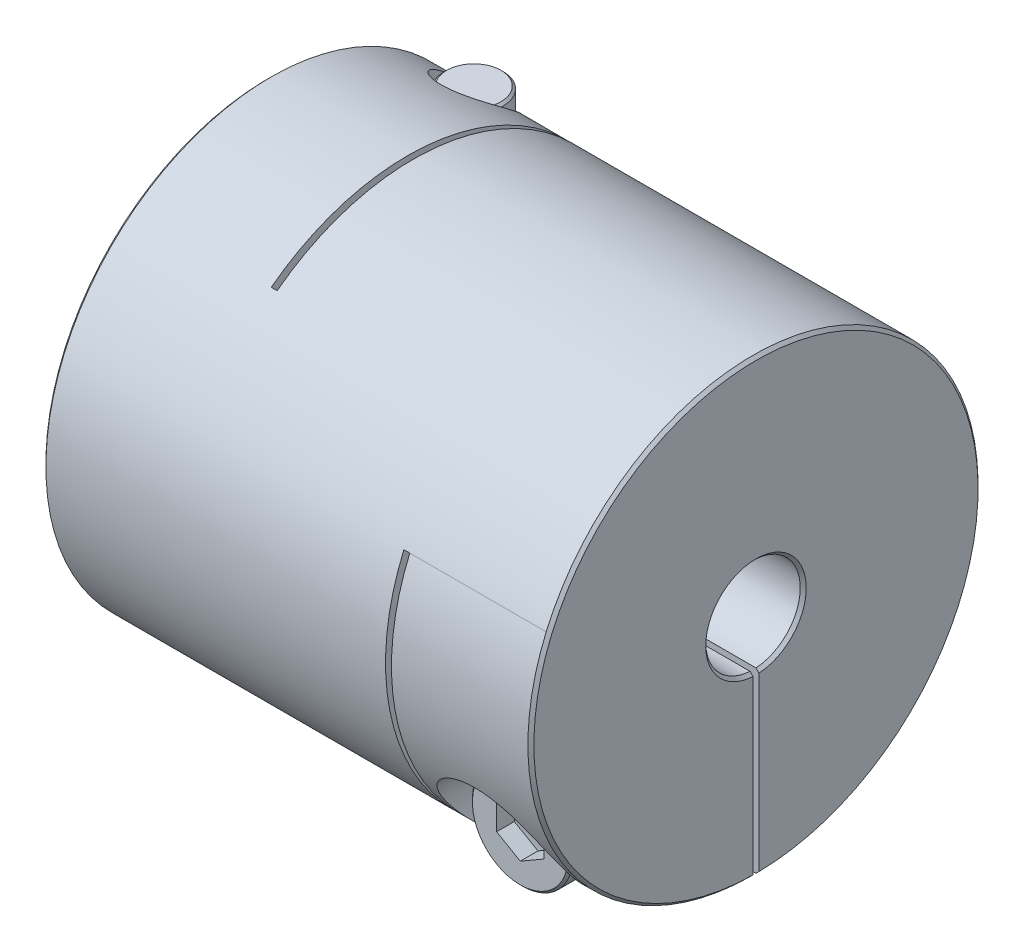
SolidWorks part; units mm, degrees
ref_plane "Front Plane" through (0, 0, 0) normal (0, 0, 1) x (1, 0, 0)
ref_plane "Top Plane" through (0, 0, 0) normal (0, 1, 0) x (1, 0, 0)
ref_plane "Right Plane" through (0, 0, 0) normal (1, 0, 0) x (0, 0, -1)
sketch "Sketch1" plane through (0, 0, 0) normal (1, 0, 0) x (0, 0, -1)
  circle A0 centre (0, 0) radius 19.05
  dimension "dim D" = 38.1
extrude "Boss-Extrude1" add sketch "Sketch1" along normal mid plane 41.3
sketch "Sketch2" plane through (20.65, 0, 0) normal (1, 0, 0) x (0, 0, -1)
  circle A0 centre (0, 0) radius 4
  dimension "dim D1" = 8
extrude "Cut-Extrude1" cut sketch "Sketch2" against normal through all
chamfer "Chamfer1" distance 0.254 angle 45 4 edges at (-20.65, 0, -4) (-20.65, 0, -19.05) (20.65, 0, -19.05) (20.65, 0, -4)
ref_plane "Plane2" through (0, -19.05, 0) normal (0, -1, 0) x (1, 0, 0)
ref_plane "L1" through (-14.75, 0, 0) normal (-1, 0, 0) x (0, 0, 1)
sketch "Sketch4" plane through (0, -19.05, 0) normal (0, -1, 0) x (1, 0, 0)
  line L0 (-20.396, -19.05) -> (20.396, -19.05) construction
  line L1 (-8.85, -19.05) -> (-8.35, -19.05)
  line L2 (-8.85, -19.05) -> (-8.85, 11.525)
  line L3 (-8.85, 11.525) -> (-8.35, 11.525)
  line L4 (-8.35, -19.05) -> (-8.35, 11.525)
  line L5 (-8.85, 4) -> (-8.85, 19.05) construction
  line L6 (20.396, 4) -> (-20.396, 4) construction
  line L7 (20.396, 19.05) -> (-20.396, 19.05) construction
  line L10 (-8.85, 11.525) -> (-20.65, 11.525) construction
  line L11 (-20.65, 18.796) -> (-20.65, -18.796) construction
  line L12 (-14.75, 10.2256) -> (-14.75, -10.2256) construction
  point P16 (-14.75, 11.525)
  dimension "D1" = 0.5
extrude "Cut-Extrude2" cut sketch "Sketch4" against normal through all
ref_plane "Plane4" through (0, 0, -19.05) normal (0, 0, -1) x (-1, 0, 0)
sketch "Sketch7" plane through (0, 0, -19.05) normal (0, 0, -1) x (-1, 0, 0)
  line L1 (-8.35, -19.05) -> (-8.85, -19.05)
  line L2 (-8.85, -19.05) -> (-8.85, 7.525)
  line L3 (-8.85, 7.525) -> (-8.35, 7.525)
  line L4 (-8.35, -19.05) -> (-8.35, 7.525)
  line L5 (20.65, 8.6487) -> (14.75, 8.6487) construction
  line L7 (-10.505, -19.05) -> (10.505, -19.05) construction
  line L8 (-20.396, -4) -> (8.35, -4) construction
  line L9 (20.65, -18.796) -> (20.65, 18.796) construction
  line L10 (-20.396, -4) -> (8.35, -4) construction
  line L11 (8.35, 15.1683) -> (8.85, 15.1683) construction
  line L12 (-8.85, 7.525) -> (-8.85, -19.05) construction
  line L14 (-20.396, -4) -> (8.35, -4) construction
  line L16 (-20.396, -4) -> (8.35, -4) construction
  line L17 (8.85, -19.05) -> (20.396, -19.05) construction
  line L18 (14.75, -10.2256) -> (14.75, 10.2256) construction
  line L19 (-20.396, -19.05) -> (-20.396, 19.05) construction
  line L20 (-20.65, 7.525) -> (-14.75, 7.525) construction
  line L21 (-20.65, 18.796) -> (-20.65, -18.796) construction
  line L22 (-14.75, 7.525) -> (-8.85, 7.525) construction
  line L23 (-20.396, -19.05) -> (-20.396, 19.05) construction
  line L24 (-20.396, -4) -> (-20.396, 19.05) construction
  line L25 (-20.396, -4) -> (8.35, -4) construction
  point P23 (-8.85, 7.525)
  point P33 (-20.396, 7.525)
extrude "Cut-Extrude3" cut sketch "Sketch7" against normal through all
sketch "Sketch8" plane through (0, 0, 0) normal (0, 1, 0) x (1, 0, 0)
  line L0 (-8.85, -11.525) -> (-8.85, 19.05) construction
  line L1 (-20.65, 19.05) -> (-8.85, 19.05)
  line L2 (-20.65, 19.05) -> (-20.65, 0)
  line L3 (-20.65, 0) -> (-8.85, 0)
  line L4 (-8.85, 19.05) -> (-8.85, 0)
  line L5 (10.505, 19.05) -> (-10.505, 19.05) construction
  line L6 (-20.65, 18.796) -> (-20.65, -18.796) construction
extrude "Cut-Extrude5" cut sketch "Sketch8" against normal mid plane 0.5
sketch "Sketch13" plane through (0, 0, 0) normal (0, 0, 1) x (1, 0, 0)
  line L0 (20.65, -18.796) -> (20.65, 18.796) construction
  line L1 (8.85, -19.05) -> (20.65, -19.05)
  line L2 (8.85, -19.05) -> (8.85, 0)
  line L3 (8.85, 0) -> (20.65, 0)
  line L4 (20.65, -19.05) -> (20.65, 0)
extrude "Cut-Extrude6" cut sketch "Sketch13" against normal mid plane 0.5
hole_wizard "CBORE for M5 SHCS1" positions "Sketch12" profile "Sketch11" counterbore size "M5" standard "Ansi Metric" end condition through all
sketch "Sketch12" plane through (0, -19.05, 0) normal (0, -1, 0) x (1, 0, 0)
  line L0 (-14.75, 10.2256) -> (-14.75, -10.2256) construction
  line L1 (-8.85, -3.9922) -> (-8.85, -19.0484) construction
  line L2 (-8.85, -3.9922) -> (-8.85, -19.0484)
  line L3 (-8.85, -11.5203) -> (-14.75, -11.5203) construction
  point P0 (-14.75, -11.5203)
sketch "Sketch11" plane through (-14.75, -19.05, -11.5203) normal (1, 0, 0) x (0, 0, -1)
  line L0 (0, 0) -> (0, 38.1)
  line L1 (0, 38.1) -> (2.75, 38.1)
  line L3 (2.75, 38.1) -> (2.75, 10)
  line L4 (2.75, 10) -> (5, 10)
  line L5 (5, 10) -> (5, 0)
  line L7 (5, 0) -> (0, 0)
  line L11 (0, -6.35) -> (0, 107.95) construction
  dimension "Thru Hole Dia." = 5.5
  dimension "Thru Hole Depth" = 38.1
  dimension "C'Bore Dia." = 10
  dimension "C'Bore Depth" = 10
ref_plane "Plane5" through (0, 0, 19.05) normal (0, 0, 1) x (1, 0, 0)
hole_wizard "CBORE for M5 SHCS2" positions "Sketch15" profile "Sketch14" counterbore size "M5" standard "Ansi Metric" end condition through all
sketch "Sketch15" plane through (0, 0, 19.05) normal (0, 0, 1) x (1, 0, 0)
  line L0 (-19.75, -9.05) -> (-9.75, -9.05) construction
  line L1 (-19.75, -9.05) -> (-9.75, -9.05)
  line L5 (0, 0) -> (0, 19.05) construction
  line L6 (-8.85, 19.05) -> (-20.396, 19.05) construction
  line L8 (19.75, -9.05) -> (9.75, -9.05)
  line L9 (14.75, -9.05) -> (14.75, -11.5203) construction
  line L11 (14.75, -19.0484) -> (14.75, -3.9922) construction
  line L12 (20.396, -19.0484) -> (8.85, -19.0484) construction
  line L13 (8.85, -3.9922) -> (20.396, -3.9922) construction
  point P0 (14.75, -11.5203)
sketch "Sketch14" plane through (14.75, -11.5203, 19.05) normal (1, 0, 0) x (0, -1, 0)
  line L0 (0, 0) -> (0, 38.1)
  line L1 (0, 38.1) -> (2.75, 38.1)
  line L3 (2.75, 38.1) -> (2.75, 10)
  line L4 (2.75, 10) -> (5, 10)
  line L5 (5, 10) -> (5, 0)
  line L7 (5, 0) -> (0, 0)
  line L11 (0, -6.35) -> (0, 107.95) construction
  dimension "Thru Hole Dia." = 5.5
  dimension "Thru Hole Depth" = 38.1
  dimension "C'Bore Dia." = 10
  dimension "C'Bore Depth" = 10
sketch "Sketch16" plane through (0, 0, 9.05) normal (0, 0, 1) x (1, 0, 0)
  circle A0 centre (14.75, -11.5203) radius 4.25
  dimension "screw dia" = 8.5
extrude "Boss-Extrude2" add sketch "Sketch16" along normal blind 5 separate body
sketch "Sketch17" plane through (0, 0, 9.05) normal (0, 0, -1) x (-1, 0, 0)
  circle A0 centre (-14.75, -11.5203) radius 2.5
  dimension "D1" = 5
extrude "Boss-Extrude3" add sketch "Sketch17" along normal blind 24.5
chamfer "Chamfer2" distance 0.2 angle 45 3 edges at (12.25, -11.5203, -15.45) (19, -11.5203, 9.05) (19, -11.5203, 14.05)
sketch "Sketch18" plane through (0, 0, 14.05) normal (0, 0, 1) x (1, 0, 0)
  line L1 (14.75, -13.8297) -> (16.75, -12.675)
  line L2 (16.75, -12.675) -> (16.75, -10.3656)
  line L3 (16.75, -10.3656) -> (14.75, -9.2109)
  line L4 (14.75, -9.2109) -> (12.75, -10.3656)
  line L5 (12.75, -10.3656) -> (12.75, -12.675)
  line L6 (12.75, -12.675) -> (14.75, -13.8297)
  circle A0 centre (14.75, -11.5203) radius 2 construction
  dimension "hex" = 4
extrude "Cut-Extrude7" cut sketch "Sketch18" against normal blind 1.5
mirror "Mirror1" about plane through (0, 0, 0) normal (1, 0, 0) of bodies 121
pattern_circular "CirPattern1" count 2 every 90 about axis through (0, 0, 0) along (1, 0, 0) of bodies 122
delete or keep bodies "Body-Delete1" type delete bodies bodies 122
